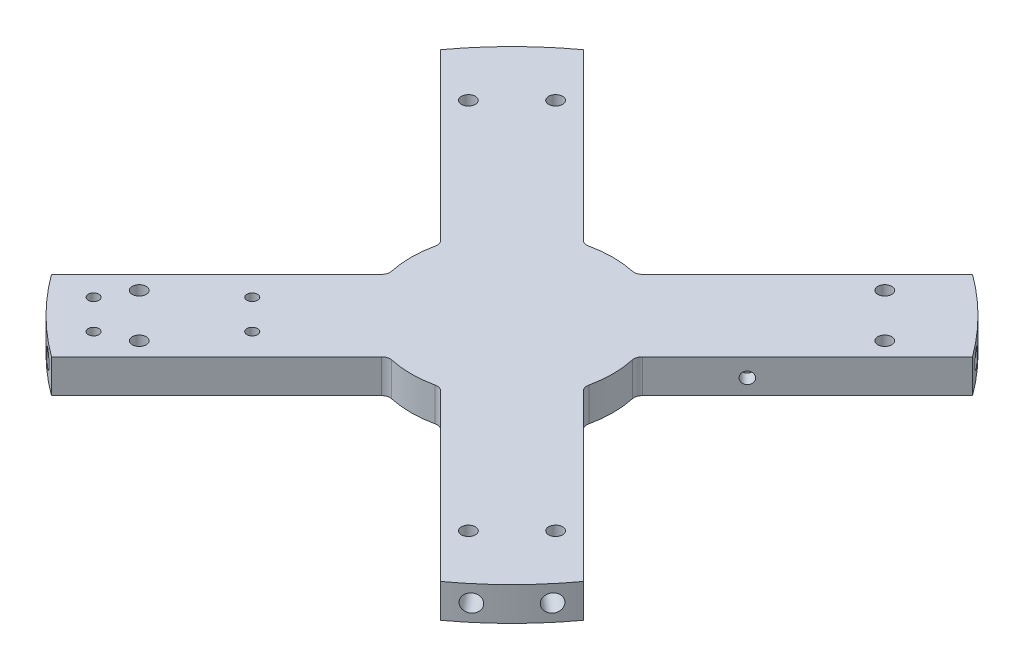
SolidWorks part; units mm, degrees
other "DetailItem1"
other "DetailItem2"
other "DetailItem3"
other "DetailItem4"
other "DetailItem5"
other "DetailItem6"
other "DetailItem7"
other "DetailItem8"
other "Weld Folder"
material "6061-T6 (SS)"
ref_plane "Front Plane" through (0, 0, 0) normal (0, 0, 1) x (1, 0, 0)
ref_plane "Top Plane" through (0, 0, 0) normal (0, 1, 0) x (1, 0, 0)
ref_plane "Right Plane" through (0, 0, 0) normal (1, 0, 0) x (0, 0, -1)
sketch "Sketch5" plane through (0, 0, 0) normal (0, 1, 0) x (1, 0, 0)
  line L48 (-0.0346, 0.0346) -> (0.0346, -0.0346) construction
  line L53 (0, 0) -> (-103.2729, -103.2729) construction
  line L55 (-19.2429, 19.2429) -> (19.2429, -19.2429) construction
  line L56 (-11.8332, -44.1621) -> (-88.1081, -120.437)
  line L58 (-44.1621, -11.8332) -> (-120.437, -88.1081)
  line L59 (-49.9706, -82.2996) -> (-82.2996, -49.9706) construction
  line L60 (-44.1621, 11.8332) -> (-120.437, 88.1081)
  line L61 (-11.8332, 44.1621) -> (-88.1081, 120.437)
  line L62 (11.8332, 44.1621) -> (88.1081, 120.437)
  line L63 (44.1621, 11.8332) -> (120.437, 88.1081)
  line L64 (44.1621, -11.8332) -> (120.437, -88.1081)
  line L65 (11.8332, -44.1621) -> (88.1081, -120.437)
  line L66 (-88.1081, 120.437) -> (0, 0) construction
  line L67 (0, 0) -> (-120.437, 88.1081) construction
  arc A0 (-88.1081, -120.437) -> (-120.437, -88.1081) centre (0, 0) cw
  arc A1 (-44.1621, 11.8332) -> (-44.1621, -11.8332) centre (0, 0) ccw
  arc A2 (11.8332, 44.1621) -> (-11.8332, 44.1621) centre (0, 0) ccw
  arc A3 (-120.437, 88.1081) -> (-88.1081, 120.437) centre (0, 0) cw
  arc A4 (44.1621, -11.8332) -> (44.1621, 11.8332) centre (0, 0) ccw
  arc A5 (88.1081, 120.437) -> (120.437, 88.1081) centre (0, 0) cw
  arc A6 (-11.8332, -44.1621) -> (11.8332, -44.1621) centre (0, 0) ccw
  arc A7 (120.437, -88.1081) -> (88.1081, -120.437) centre (0, 0) cw
  point P32 (0, 0)
  dimension "D3" = 149.225
  dimension "D5" = 45.72
  dimension "D1" = 90
  dimension "D2" = 146.05
  dimension "D4" = 45.72
  dimension "D6" = 4
extrude "Boss-Extrude3" add sketch "Sketch5" along normal blind 15.24
sketch "Sketch6" plane through (0, 15.24, 0) normal (0, 1, 0) x (1, 0, 0)
  line L0 (0, 0) -> (-84.4144, -84.4144) construction
  line L1 (-84.4144, -84.4144) -> (-74.5361, -94.2927) construction
  line L3 (0, 174.0525) -> (0, -174.0525) construction
  line L4 (0, 0) -> (102.9231, 0) construction
  circle A27 centre (-74.5361, -94.2927) radius 3.175
  circle A46 centre (-94.2927, -74.5361) radius 3.175
  circle A64 centre (94.2927, -74.5361) radius 3.175
  circle A65 centre (74.5361, -94.2927) radius 3.175
  circle A66 centre (94.2927, 74.5361) radius 3.175
  circle A67 centre (74.5361, 94.2927) radius 3.175
  circle A68 centre (-94.2927, 74.5361) radius 3.175
  circle A69 centre (-74.5361, 94.2927) radius 3.175
  point P23 (0, 0)
  point P24 (0, 0)
  dimension "D2" = 6.35
  dimension "D1" = 13.97
  dimension "D3" = 119.38
  dimension "D4" = 45
extrude "Cut-Extrude2" cut sketch "Sketch6" against normal through all
sketch "Sketch46" plane through (0, 0, 0) normal (0, -1, 0) x (1, 0, 0)
  line L0 (-77.7111, 94.2927) -> (-94.2927, 77.7111)
  line L1 (-94.2927, 77.7111) -> (-91.1177, 74.5361)
  line L2 (-91.1177, 74.5361) -> (-74.5361, 91.1177)
  line L3 (-74.5361, 91.1177) -> (-77.7111, 94.2927)
  line L4 (0, 0) -> (173.749, 0) construction
  line L9 (-74.5361, -91.1177) -> (-77.7111, -94.2927)
  line L18 (-91.1177, -74.5361) -> (-74.5361, -91.1177)
  line L19 (-94.2927, -77.7111) -> (-91.1177, -74.5361)
  line L20 (-77.7111, -94.2927) -> (-94.2927, -77.7111)
  line L21 (0, 0) -> (0, 139.7657) construction
  line L22 (77.7111, -94.2927) -> (94.2927, -77.7111)
  line L23 (94.2927, -77.7111) -> (91.1177, -74.5361)
  line L24 (91.1177, -74.5361) -> (74.5361, -91.1177)
  line L25 (74.5361, -91.1177) -> (77.7111, -94.2927)
  line L26 (74.5361, 91.1177) -> (77.7111, 94.2927)
  line L27 (91.1177, 74.5361) -> (74.5361, 91.1177)
  line L28 (94.2927, 77.7111) -> (91.1177, 74.5361)
  line L29 (77.7111, 94.2927) -> (94.2927, 77.7111)
  circle A0 centre (-74.5361, 94.2927) radius 3.175 construction
  circle A1 centre (-94.2927, 74.5361) radius 3.175 construction
split line "Split Line4"
sketch "Sketch53" plane through (0, 15.24, 0) normal (0, 1, 0) x (1, 0, 0)
  line L1 (-44.1621, -11.8332) -> (-120.437, -88.1081) construction
  line L2 (11.8332, -44.1621) -> (88.1081, -120.437) construction
  line L3 (-120.437, 88.1081) -> (-44.1621, 11.8332) construction
  circle A0 centre (-88.4555, -101.0279) radius 2.413
  circle A1 centre (-52.5345, -65.1069) radius 2.413
  circle A2 centre (-101.9259, -87.5575) radius 2.413
  circle A3 centre (-66.0049, -51.6365) radius 2.413
  dimension "D7" = 4.826
  dimension "D1" = 19.05
  dimension "D2" = 19.05
  dimension "D3" = 50.8
  dimension "D4" = 12.7
  dimension "D5" = 12.7
  dimension "D6" = 50.8
  dimension "D8" = 60.325
  dimension "D9" = 60.325
extrude "Cut-Extrude6" cut sketch "Sketch53" against normal up to next contours A0 | A1 | A3 | A2
sketch "Sketch56" plane through (0, 15.24, 0) normal (0, 1, 0) x (1, 0, 0)
  line L0 (0, 0) -> (85.7157, 102.152) construction
  line L1 (0, 0) -> (-176.5821, 0) construction
  line L2 (0, 0) -> (-165.1308, -165.1308) construction
  line L3 (0, 0) -> (102.152, 85.7157) construction
  dimension "D1" = 5
  dimension "D2" = 45
ref_plane "Plane1" through (-95.92, 0, 114.313) normal (-0.6428, 0, 0.766) x (0.766, 0, 0.6428)
ref_plane "Plane2" through (-114.313, 0, 95.92) normal (-0.766, 0, 0.6428) x (0.6428, 0, 0.766)
sketch "Sketch55" plane through (-95.92, 0, 114.313) normal (-0.6428, 0, 0.766) x (0.766, 0, 0.6428)
  line L0 (0, 7.62) -> (0, 0) construction
  line L1 (0, 7.62) -> (0, 15.24) construction
  line L2 (-34729.6355, 15.24) -> (34752.7915, 15.24) construction
  circle A0 centre (0, 7.62) radius 3.9688
  dimension "D1" = 7.9375
fillet "Fillet1" radius 3.81 8 edges at (-11.8332, 7.62, 44.1621) (11.8332, 7.62, 44.1621) (-44.1621, 7.62, 11.8332) (-44.1621, 7.62, -11.8332) (-11.8332, 7.62, -44.1621) (11.8332, 7.62, -44.1621) (44.1621, 7.62, -11.8332) (44.1621, 7.62, 11.8332)
sketch "Sketch57" plane through (-114.313, 0, 95.92) normal (-0.766, 0, 0.6428) x (0.6428, 0, 0.766)
  line L0 (-19.1354, 7.62) -> (35.6253, 7.62) construction
  line L1 (-19.1354, 15.24) -> (-19.1354, 0) construction
  line L2 (35.6253, 15.24) -> (35.6253, 0) construction
  line L3 (0, 0) -> (0, 15.24) construction
  line L4 (34729.6355, 15.24) -> (-34752.7915, 15.24) construction
  circle A1 centre (0, 7.62) radius 3.9688
  dimension "D1" = 7.9375
extrude "Cut-Extrude8" cut sketch "Sketch57" against normal blind 11.43
extrude "Cut-Extrude9" cut sketch "Sketch55" against normal blind 11.43
pattern_circular "CirPattern2" count 4 over 360 about axis through (0, 0, 0) along (0, 1, 0) of "Cut-Extrude9", "Cut-Extrude8"
ref_plane "Plane3" through (-105.518, 0, 105.518) normal (-0.7071, 0, 0.7071) x (0.7071, 0, 0.7071)
sketch "Sketch59" plane through (-16.1645, 0, -16.1645) normal (-0.7071, 0, -0.7071) x (-0.7071, 0, 0.7071)
  circle A0 centre (-75.3632, 6.985) radius 2.6055
extrude "Cut-Extrude11" cut sketch "Sketch59" against normal blind 6.35
sketch "Sketch60" plane through (16.1645, 0, 16.1645) normal (0.7071, 0, 0.7071) x (0.7071, 0, -0.7071)
  circle A0 centre (75.3632, 6.985) radius 2.6606
extrude "Cut-Extrude12" cut sketch "Sketch60" against normal blind 6.35
sketch "Sketch62" plane through (0, 0, 0) normal (0, -1, 0) x (1, 0, 0)
  circle A0 centre (93.8949, -94.405) radius 2.54
extrude "Cut-Extrude14" cut sketch "Sketch62" against normal blind 3.81
equation "\"Rocket Diameter\"= 12"
equation "\"Rocket Thickness\"= .25"
equation "\"Plate_Mount\"= \"Rocket Diameter\" - 6 * \"Rocket Thickness\""
equation "\"Beam_Thickness\"= \"Rocket Diameter\" / 20"
equation "\"Cord Diameter\"=0.25"
equation "\"Center_Circle\"= \"Rocket Diameter\" / 12"
equation "\"D1@Sketch6\"=\"Beam_Thickness\"/2+\"Cord Diameter\""
equation "\"D2@Sketch6\"=\"Cord Diameter\""
equation "\"D3@Sketch6\"= \"Inner Radius\" * 4 / 5"
equation "\"Shear Pin Distance\"= 2"
equation "\"D2@Sketch5\"=(\"Rocket Diameter\"/2)-\"Rocket Thickness\""
equation "\"D3@Sketch5\"= \"Inner Radius\""
equation "\"D4@Sketch5\"=\"Beam_Thickness\"*3"
equation "\"D5@Sketch5\"=\"Beam_Thickness\"*3"
equation "\"Center Radius\"= ( \"Beam_Thickness\" * 4 * .75 + .25 * ( \"Plate_Mount\" / 2 ) ) / 2"
equation "\"Inner Radius\"= ( \"Rocket Diameter\" - \"Rocket Thickness\" ) * 0.5"
